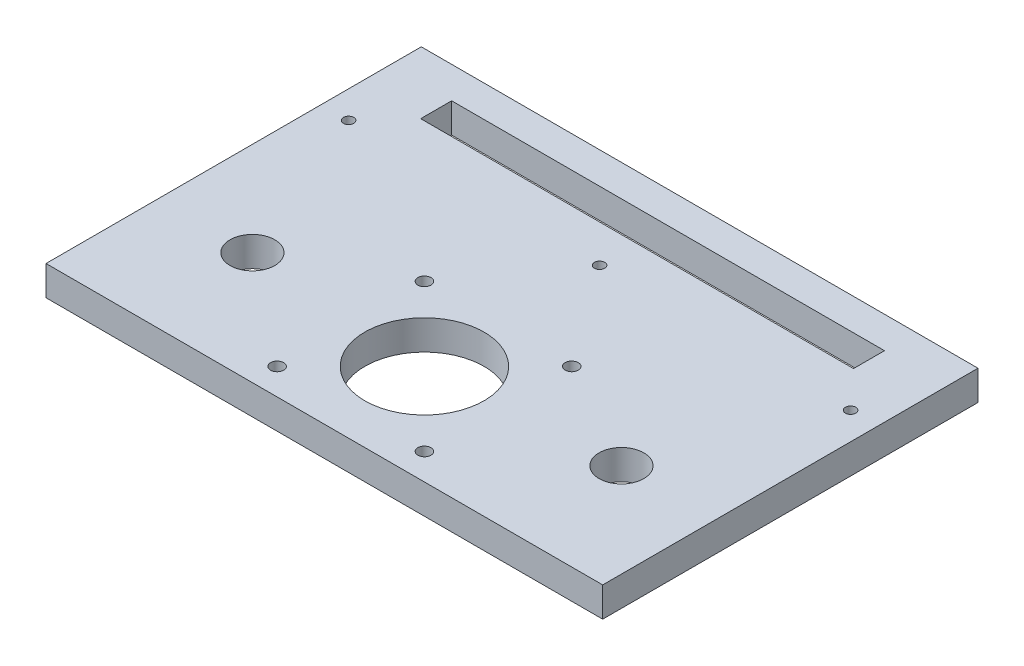
SolidWorks part; units mm, degrees
ref_plane "Front Plane" through (0, 0, 0) normal (0, 0, 1) x (1, 0, 0)
ref_plane "Top Plane" through (0, 0, 0) normal (0, 1, 0) x (1, 0, 0)
ref_plane "Right Plane" through (0, 0, 0) normal (1, 0, 0) x (0, 0, -1)
sketch "Sketch1" plane through (0, 0, 0) normal (0, 1, 0) x (1, 0, 0)
  line L2 (-89, 60) -> (-89, -60)
  line L3 (-89, -60) -> (89, -60)
  line L4 (89, 60) -> (89, -60)
  line L5 (-89, 60) -> (89, -60) construction
  line L6 (-89, -60) -> (89, 60) construction
  line L10 (0, -28) -> (19.05, -28) construction
  line L11 (0, -28) -> (0, -8.95) construction
  line L14 (-89, 60) -> (89, 60)
  line L15 (-69.2, 49.9) -> (-69.2, 40)
  line L16 (-69.2, 40) -> (69.2, 40)
  line L17 (69.2, 40) -> (69.2, 49.9)
  line L18 (69.2, 49.9) -> (-69.2, 49.9)
  circle A0 centre (0, -28) radius 19.05
  circle A5 centre (-59, -24) radius 7.15
  circle A6 centre (59, -24) radius 7.15
  point P0 (0, 0)
  point P7 (0, 49.9)
  point P13 (0, 60)
  dimension "D5" = 38.1
  dimension "D6" = 36
  dimension "D12" = 14.3
  dimension "D14" = 59
  dimension "D1" = 178
  dimension "D2" = 120
  dimension "D3" = 20
  dimension "D4" = 9.9
  dimension "D7" = 4
  dimension "D8" = 138.4
extrude "Boss-Extrude1" add sketch "Sketch1" along normal blind 9.5
hole_wizard "M4 Tapped Hole1" positions "Sketch2" profile "Sketch3" tap size "M4" standard "ISO" end condition through all
sketch "Sketch2" plane through (0, 9.5, 0) normal (0, 1, 0) x (1, 0, 0)
  line L1 (-89, 60) -> (-89, -60) construction
  line L2 (0, 60) -> (0, -60) construction
  line L4 (-89, -60) -> (89, -60) construction
  line L5 (-69.2, 40) -> (69.2, 40) construction
  line L6 (89, 60) -> (-89, 60) construction
  point P0 (-80.25, 28)
  point P2 (0, 28)
  point P25 (80.25, 28)
  dimension "D1" = 12
  dimension "D2" = 8.75
sketch "Sketch3" plane through (-80.25, 9.5, -28) normal (1, 0, 0) x (0, 0, 1)
  line L0 (0, 0) -> (0, 9.5)
  line L1 (0, 9.5) -> (1.65, 9.5)
  line L2 (1.65, 9.5) -> (1.65, 0)
  line L5 (1.65, 0) -> (0, 0)
  line L11 (0, -6.35) -> (0, 107.95) construction
  dimension "Thru Tap Drill Dia." = 3.3
  dimension "Thru Tap Drill Depth" = 9.5
cosmetic thread "Hole Thread1" parameters "D2"=4
cosmetic thread "Hole Thread2" parameters "D2"=4
cosmetic thread "Hole Thread3" parameters "D2"=4
hole_wizard "M5 Tapped Hole1" positions "Sketch4" profile "Sketch5" tap size "M5" standard "ISO" end condition through all
sketch "Sketch4" plane through (0, 9.5, 0) normal (0, 1, 0) x (1, 0, 0)
  circle A0 centre (0, -28) radius 19.05 construction
  point P16 (-23.55, -4.45)
  point P25 (23.55, -4.45)
  point P26 (23.55, -51.55)
  point P27 (-23.55, -51.55)
  dimension "D3" = 23.55
  dimension "D4" = 23.55
  dimension "D1" = 2
  dimension "D2" = 2
sketch "Sketch5" plane through (-23.55, 9.5, 4.45) normal (1, 0, 0) x (0, 0, 1)
  line L0 (0, 0) -> (0, 9.5)
  line L1 (0, 9.5) -> (2.1, 9.5)
  line L2 (2.1, 9.5) -> (2.1, 0)
  line L5 (2.1, 0) -> (0, 0)
  line L11 (0, -6.35) -> (0, 107.95) construction
  dimension "Thru Tap Drill Dia." = 4.2
  dimension "Thru Tap Drill Depth" = 9.5
cosmetic thread "Hole Thread4" parameters "D2"=5
cosmetic thread "Hole Thread5" parameters "D2"=5
cosmetic thread "Hole Thread6" parameters "D2"=5
cosmetic thread "Hole Thread7" parameters "D2"=5
